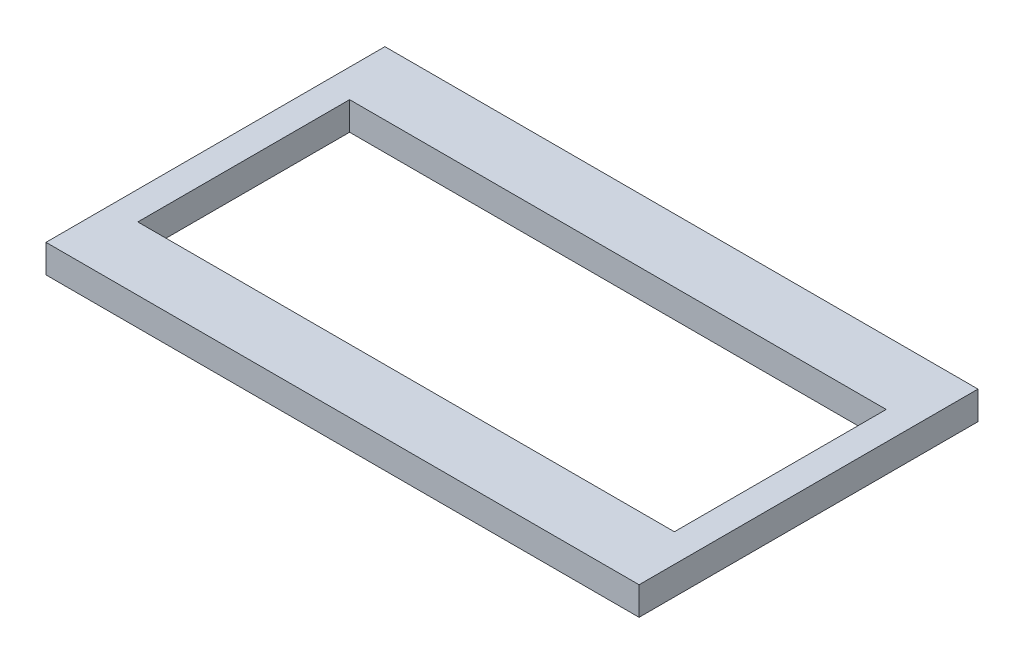
SolidWorks part; units mm, degrees
ref_plane "Front Plane" through (0, 0, 0) normal (0, 0, 1) x (1, 0, 0)
ref_plane "Top Plane" through (0, 0, 0) normal (0, 1, 0) x (1, 0, 0)
ref_plane "Right Plane" through (0, 0, 0) normal (1, 0, 0) x (0, 0, -1)
sketch "Sketch3" plane through (0, 0, 0) normal (0, 1, 0) x (1, 0, 0)
  line L1 (53.34, 30.48) -> (-53.34, 30.48)
  line L2 (53.34, 30.48) -> (53.34, -30.48)
  line L3 (53.34, -30.48) -> (-53.34, -30.48)
  line L4 (-53.34, 30.48) -> (-53.34, -30.48)
  line L5 (53.34, 30.48) -> (-53.34, -30.48) construction
  line L6 (53.34, -30.48) -> (-53.34, 30.48) construction
  line L7 (48.26, 19.05) -> (-48.26, 19.05)
  line L8 (48.26, 19.05) -> (48.26, -19.05)
  line L9 (48.26, -19.05) -> (-48.26, -19.05)
  line L10 (-48.26, 19.05) -> (-48.26, -19.05)
  line L11 (48.26, 19.05) -> (-48.26, -19.05) construction
  line L12 (48.26, -19.05) -> (-48.26, 19.05) construction
  point P0 (0, 0)
  point P6 (0, 0)
extrude "Boss-Extrude1" add sketch "Sketch3" along normal blind 5.08
